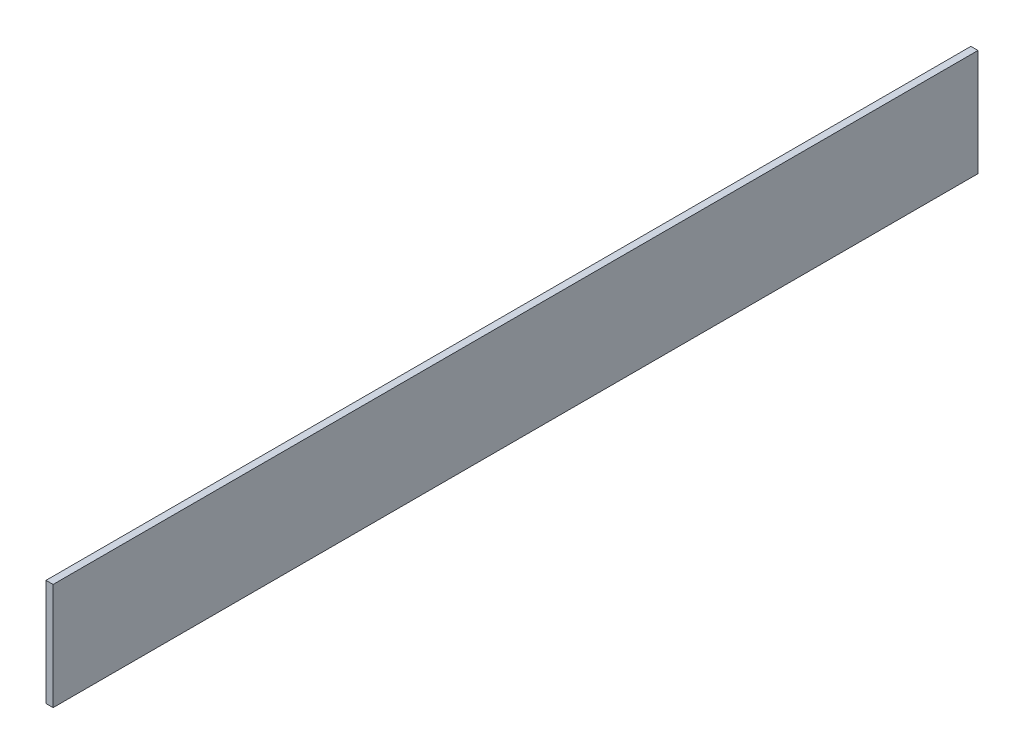
SolidWorks part; units mm, degrees
ref_plane "Ebene vorne" through (0, 0, 0) normal (0, 0, 1) x (1, 0, 0)
ref_plane "Ebene oben" through (0, 0, 0) normal (0, 1, 0) x (1, 0, 0)
ref_plane "Ebene rechts" through (0, 0, 0) normal (1, 0, 0) x (0, 0, -1)
sketch "Skizze1" plane through (0, 20, 0) normal (0, 1, 0) x (1, 0, 0)
  line L0 (150, 75) -> (150, -55)
extrude "Linear-Austragen-Dünn1" add sketch "Skizze1" along normal blind 15 thin
